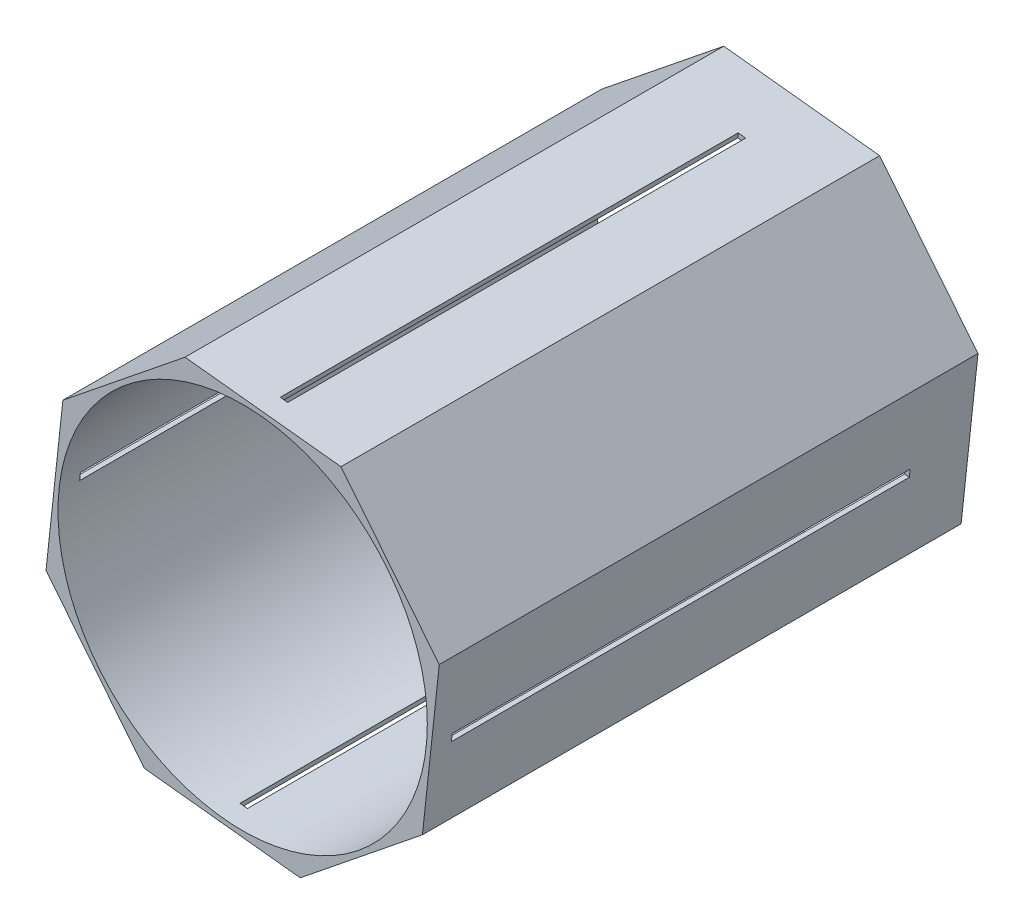
SolidWorks part; units mm, degrees
ref_plane "Front Plane" through (0, 0, 0) normal (0, 0, 1) x (1, 0, 0)
ref_plane "Top Plane" through (0, 0, 0) normal (0, 1, 0) x (1, 0, 0)
ref_plane "Right Plane" through (0, 0, 0) normal (1, 0, 0) x (0, 0, -1)
sketch "Sketch1" plane through (0, 0, 0) normal (0, 0, 1) x (1, 0, 0)
  line L0 (76.286, -41.7216) -> (83.444, 24.4407)
  line L1 (41.7216, 76.286) -> (-24.4407, 83.444)
  line L2 (-24.4407, 83.444) -> (-76.286, 41.7216)
  line L3 (-76.286, 41.7216) -> (-83.444, -24.4407)
  line L4 (-83.444, -24.4407) -> (-41.7216, -76.286)
  line L5 (-41.7216, -76.286) -> (24.4407, -83.444)
  line L6 (24.4407, -83.444) -> (76.286, -41.7216)
  line L7 (83.444, 24.4407) -> (41.7216, 76.286)
  circle A0 centre (0, 0) radius 78.359
  circle A1 centre (0, 0) radius 80.331 construction
  dimension "D1" = 156.718
extrude "Boss-Extrude1" add sketch "Sketch1" along normal blind 228.6
sketch "Sketch2" plane through (8.6404, 79.865, 0) normal (0.1076, 0.9942, 0) x (0.9942, -0.1076, 0)
  line L0 (0, 0) -> (0, -228.6) construction
  line L1 (33.2742, -228.6) -> (-33.2742, -228.6) construction
  line L3 (-1.5875, -25.4) -> (1.5875, -25.4)
  line L4 (-1.5875, -25.4) -> (-1.5875, -219.71)
  line L5 (-1.5875, -219.71) -> (1.5875, -219.71)
  line L6 (1.5875, -25.4) -> (1.5875, -219.71)
  line L7 (-1.5875, -25.4) -> (1.5875, -219.71) construction
  line L8 (-1.5875, -219.71) -> (1.5875, -25.4) construction
  point P5 (0, -122.555)
  point P10 (0, -219.71)
  dimension "D1" = 8.89
  dimension "D2" = 3.175
  dimension "D3" = 194.31
extrude "Cut-Extrude1" cut sketch "Sketch2" against normal blind 203.2
sketch "Sketch5" plane through (-79.865, 8.6404, 0) normal (-0.9942, 0.1076, 0) x (0, 0, 1)
  line L0 (0, 0) -> (228.6, 0) construction
  line L1 (0, 33.2742) -> (0, -33.2742) construction
  line L2 (228.6, 33.2742) -> (228.6, -33.2742) construction
  line L4 (25.4, -1.5875) -> (219.71, -1.5875)
  line L5 (25.4, -1.5875) -> (25.4, 1.5875)
  line L6 (25.4, 1.5875) -> (219.71, 1.5875)
  line L7 (219.71, -1.5875) -> (219.71, 1.5875)
  line L8 (25.4, -1.5875) -> (219.71, 1.5875) construction
  line L9 (25.4, 1.5875) -> (219.71, -1.5875) construction
  point P6 (122.555, 0)
  point P11 (219.71, 0)
  dimension "D1" = 8.89
  dimension "D2" = 3.175
  dimension "D3" = 194.31
extrude "Cut-Extrude2" cut sketch "Sketch5" against normal blind 203.2
